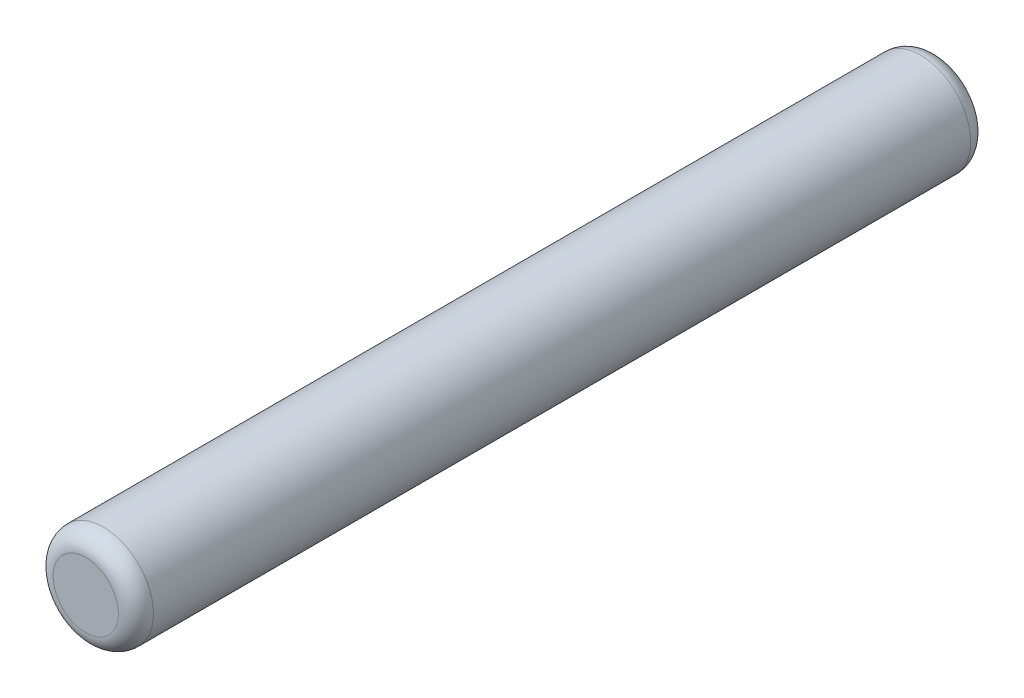
SolidWorks part; units mm, degrees
ref_plane "Front" through (0, 0, 0) normal (0, 0, 1) x (1, 0, 0)
ref_plane "Top" through (0, 0, 0) normal (0, 1, 0) x (1, 0, 0)
ref_plane "Right" through (0, 0, 0) normal (1, 0, 0) x (0, 0, -1)
sketch "Sketch1" plane through (0, 0, 0) normal (0, 0, 1) x (1, 0, 0)
  circle A0 centre (0, 0) radius 1
  dimension "D1" = 2
extrude "Boss-Extrude1" add sketch "Sketch1" along normal mid plane 17
fillet "Fillet1" radius 0.35 2 edges at (1, 0, -8.5) (1, 0, 8.5)
